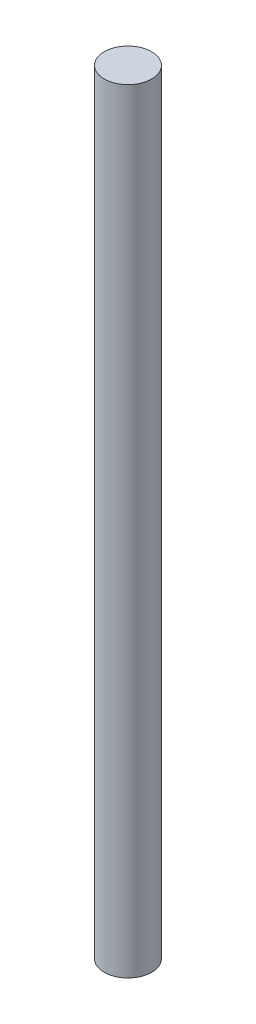
SolidWorks part; units mm, degrees
material "Chrome Stainless Steel"
ref_plane "Front Plane" through (0, 0, 0) normal (0, 0, 1) x (1, 0, 0)
ref_plane "Top Plane" through (0, 0, 0) normal (0, 1, 0) x (1, 0, 0)
ref_plane "Right Plane" through (0, 0, 0) normal (1, 0, 0) x (0, 0, -1)
sketch "Sketch1" plane through (0, 0, 0) normal (0, 1, 0) x (1, 0, 0)
  circle A0 centre (0, 0) radius 1.5
  dimension "D1" = 3
extrude "Boss-Extrude1" add sketch "Sketch1" along normal mid plane 49
scale "Scale1" scale about centroid uniform scaling yes scale factor 0.6
